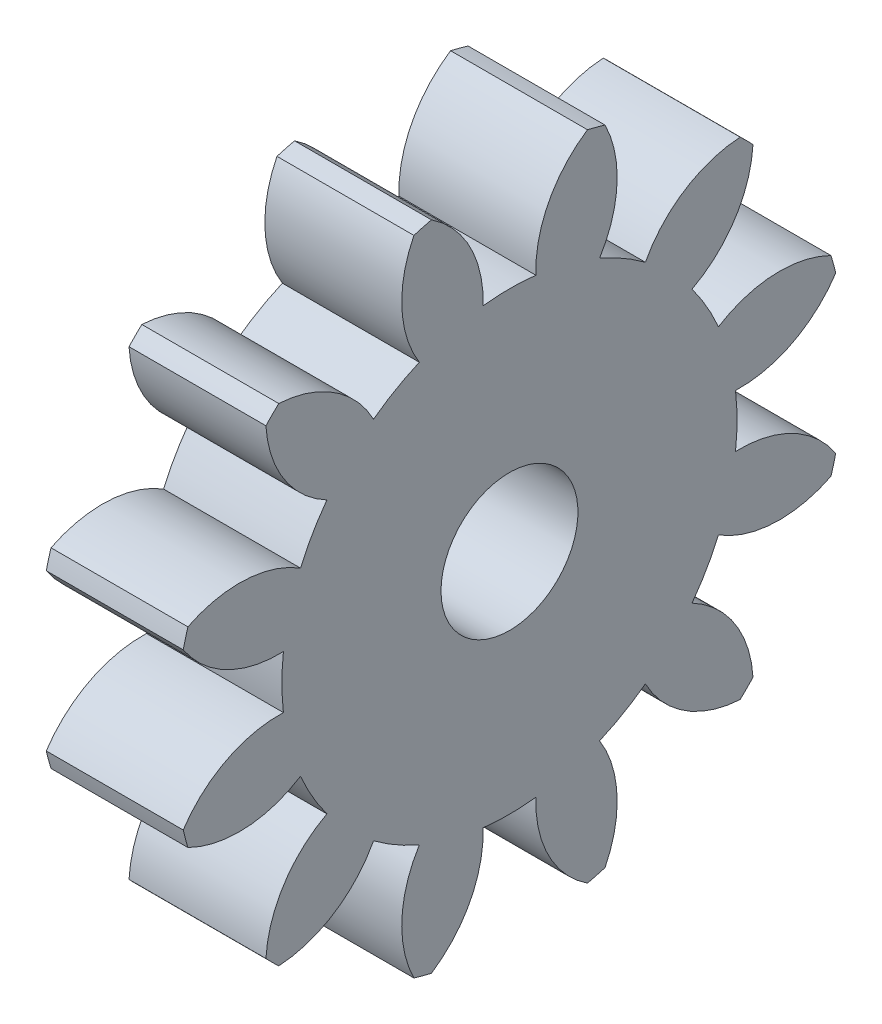
SolidWorks part; units mm, degrees
ref_plane "Plane1" through (0, 0, 0) normal (0, 0, 1) x (1, 0, 0)
ref_plane "Plane2" through (0, 0, 0) normal (0, 1, 0) x (1, 0, 0)
ref_plane "Plane3" through (0, 0, 0) normal (1, 0, 0) x (0, 0, -1)
other "Configuration Table"
sketch "HoldingSke" plane through (0, 0, 0) normal (0, 1, 0) x (1, 0, 0)
  line L0 (0, 0) -> (0.5589, -0.1188)
  line L1 (-15, 0) -> (100, 0) construction
  line L2 (0, 0) -> (-2.1039, 2.3779)
  line L3 (0, 0) -> (-11.863, 4.5341)
  line L4 (0, 0) -> (8.4473, 1.7955)
  line L5 (0, 0) -> (-46.8476, -17.4728)
  line L6 (0, 0) -> (-4.1448, -2.7965)
  line L7 (-2.1039, 2.3779) -> (8.6586, 51.2059)
  line L8 (-76.2, 54.61) -> (-75.3, 54.61)
  line L9 (-71.009, 38.7566) -> (-53.1078, 45.2721)
  line L10 (-76.2, 71.12) -> (104.1128, 71.12)
  line L11 (0, 0) -> (-5, 0)
  line L12 (-76.2, 101.6) -> (-76.147, 101.6)
  line L13 (24.9733, 27.94) -> (52.9518, 28.4284)
  line L14 (24.9733, 27.94) -> (24.9743, 27.94)
  line L15 (24.9733, 27.94) -> (100.4006, 29.5858)
  line L16 (-63.627, -1.75) -> (-12.827, -1.75)
  circle A0 centre (0, 0) radius 2.5
  circle A1 centre (0, 0) radius 8.3115
  circle A2 centre (0, 0) radius 37.5
  circle A3 centre (0, 0) radius 2.5
  dimension "MHD" = 16.623
  dimension "Hub_dia" = 75
  dimension "Bore" = 5
  dimension "MBD" = 5
  dimension "Num_teeth" = 12
  dimension "Pitch" = 0.5714
  dimension "Overall_len" = 50
  dimension "Show_teeth" = 12
  dimension "Thickness" = 5
  dimension "OAL" = 50.0001
  dimension "T_dim" = 0.9
  dimension "Ap" = 20
  dimension "H" = 19.05
  dimension "Pitch_radius" = 180.3128
  dimension "Width" = 5
  dimension "Backlash" = 0.053
  dimension "Addendum_fac" = 1
  dimension "Dedendum_fac" = 1.25
  dimension "Clearance_fac" = 0.25
  dimension "Dedendum_add" = 0.001
  dimension "Module" = 1.75
sketch "BasProSke" plane through (0, 0, 0) normal (0, 1, 0) x (1, 0, 0)
  line L0 (-10, 0) -> (60, 0) construction
  line L1 (0, 0) -> (0, 12.25)
  line L2 (0, 0) -> (5, 0)
  line L3 (5, 0) -> (5, 12.25)
  line L4 (5, 12.25) -> (0, 12.25)
  dimension "Thickness" = 5
  dimension "Diameter" = 24.5
revolve "Base-Revolve" add sketch "BasProSke" angle 360 about L0
sketch "TooCutSke" plane through (0, 0, 0) normal (1, 0, 0) x (0, 0, -1)
  line L1 (0, 0) -> (0, 107) construction
  line L2 (0, 0) -> (-1.4632, 10.3976) construction
  line L3 (0, 0) -> (-5.3948, 20.1337) construction
  line L4 (-1.4632, 10.3976) -> (-2.6974, 10.0668) construction
  arc A0 (0.9651, 8.2553) -> (-0.9651, 8.2553) centre (0, 0) ccw
  arc A1 (2.8783, 11.9332) -> (-2.8783, 11.9332) centre (0, 0) ccw
  circle A2 centre (0, 0) radius 10.5 construction
  circle A3 centre (0, 0) radius 9.8668 construction
  arc A4 (-0.9651, 8.2553) -> (-2.8783, 11.9332) centre (-5.1623, 8.4085) ccw
  arc A5 (2.8783, 11.9332) -> (0.9651, 8.2553) centre (5.1623, 8.4085) ccw
  dimension "Root_dia" = 16.623
  dimension "Overcut_dia" = 24.5508
  dimension "Pitch_dia" = 21
  dimension "Base_dia" = 19.7335
  dimension "Flank_rad" = 4.2
  dimension "Half_ang" = 15
  dimension "Half_CT" = 1.2778
extrude "ToothCut" cut sketch "TooCutSke" along normal through all
fillet "Breaks" [suppressed] radius 0.035
fillet "RootFillets" [suppressed] radius 0.4385
pattern_circular "TeethCuts" count 12 every 30 about axis through (-10, 0, 0) along (1, 0, 0) of "ToothCut", "RootFillets", "Breaks"
sketch "HubNeaOneSke" plane through (0, 0, 0) normal (-1, 0, 0) x (0, 0, 1)
  circle A0 centre (0, 0) radius 8.3115
  dimension "Diameter" = 16.623
extrude "HubNearOne" [suppressed] add sketch "HubNeaOneSke" along normal blind 45.0001
sketch "HubNeaBotSke" plane through (0, 0, 0) normal (-1, 0, 0) x (0, 0, 1)
  circle A0 centre (0, 0) radius 8.3115
  dimension "Diameter" = 16.623
extrude "HubNearBoth" [suppressed] add sketch "HubNeaBotSke" along normal blind 22.5
ref_plane "FarPln" through (5, 0, 0) normal (1, 0, 0) x (0, 0, -1)
sketch "HubFarSke" plane through (5, 0, 0) normal (1, 0, 0) x (0, 0, -1)
  circle A0 centre (0, 0) radius 8.3115
  dimension "Diameter" = 16.623
extrude "HubFar" [suppressed] add sketch "HubFarSke" along normal blind 22.5
sketch "BorSke" plane through (0, 0, 0) normal (1, 0, 0) x (0, 0, -1)
  circle A0 centre (0, 0) radius 2.5
  dimension "Diameter" = 5
extrude "Bore" cut sketch "BorSke" along normal mid plane 100.0001
sketch "KeySke" plane through (0, 0, 0) normal (1, 0, 0) x (0, 0, -1)
  line L0 (-1, 0) -> (-1, 3.4)
  line L1 (-1, 3.4) -> (1, 3.4)
  line L2 (1, 3.4) -> (1, 0)
  line L3 (0, 0) -> (0, 34) construction
  line L4 (-1, 0) -> (1, 0)
  dimension "Offset" = 3.4
  dimension "Width" = 2
extrude "Keyway" [suppressed] cut sketch "KeySke" along normal mid plane 100.0001
pattern_circular "Keyway2" [suppressed] count 2 every 90 about axis through (-10, 0, 0) along (1, 0, 0)
equation "' \"Module@HoldingSke\" = 6.35"
equation "' \"Num_teeth@HoldingSke\" = 12"
equation "' \"Ap@HoldingSke\" =  20"
equation "' \"Ap@HoldingSke\" = 20"
equation "' \"Width@HoldingSke\" = 0.5 * 25.4"
equation "' \"Hub_dia@HoldingSke\"= 1 * 25.4"
equation "' \"Hub_dia@HoldingSke\" = 1 * 25.4"
equation "' \"Overall_len@HoldingSke\" = 1.0 * 25.4"
equation "' \"Bore@HoldingSke\" = 0.75 * 25.4"
equation "' \"T_dim@HoldingSke\" = 0.1 * 25.4"
equation "' \"Width@KeySke\" = 0.25 * 25.4"
equation "' \"Show_teeth@HoldingSke\" = 13"
equation "' \"Backlash@HoldingSke\" = 0.009 * 25.4"
equation "' \"Addendum_fac@HoldingSke\" = 1.0"
equation "' \"Dedendum_fac@HoldingSke\" = 1.25"
equation "' \"Dedendum_add@HoldingSke\" = 0.00005 * 25.4"
equation "' \"Clearance_fac@HoldingSke\" = 0.25"
equation "\"Pitch@HoldingSke\" = 1 / \"Module@HoldingSke\""
equation "\"Overcut_dia@TooCutSke\" = (\"Num_teeth@HoldingSke\" + 2 * \"Addendum_fac@HoldingSke\") / \"Pitch@HoldingSke\" + 0.002 * 25.4"
equation "\"Pitch_dia@TooCutSke\" = \"Num_teeth@HoldingSke\" / \"Pitch@HoldingSke\""
equation "\"Base_dia@TooCutSke\" = \"Num_teeth@HoldingSke\" / \"Pitch@HoldingSke\" * cos((\"Ap@HoldingSke\"  * 3.14159265 / 180))"
equation "\"Root_dia@TooCutSke\" = (\"Num_teeth@HoldingSke\" + 2) / \"Pitch@HoldingSke\" - 2 * (\"Addendum_fac@HoldingSke\" + \"Dedendum_fac@HoldingSke\") / \"Pitch@HoldingSke\" - \"Dedendum_add@HoldingSke\" * 2"
equation "\"Half_ang@TooCutSke\" = 180 / \"Num_teeth@HoldingSke\""
equation "\"Half_CT@TooCutSke\" = \"Num_teeth@HoldingSke\" / \"Pitch@HoldingSke\" * sin((3.14159265 / 2 / \"Num_teeth@HoldingSke\")) / 2 - 7 * \"Backlash@HoldingSke\" / 4"
equation "\"Flank_rad@TooCutSke\" = \"Num_teeth@HoldingSke\" / \"Pitch@HoldingSke\" / 5"
equation "\"Radius@RootFillets\" = \"Clearance_fac@HoldingSke\" / \"Pitch@HoldingSke\" + \"Dedendum_add@HoldingSke\""
equation "\"Break_rad@Breaks\" = 0.02 / \"Pitch@HoldingSke\""
equation "\"Thickness@HoldingSke\" = \"Width@HoldingSke\""
equation "\"OAL@HoldingSke\" = \"Thickness@HoldingSke\""
equation "\"MHD@HoldingSke\" = (\"Num_teeth@HoldingSke\" + 2) / \"Pitch@HoldingSke\" - 2 * (\"Addendum_fac@HoldingSke\" + \"Dedendum_fac@HoldingSke\")  / \"Pitch@HoldingSke\" - \"Dedendum_add@HoldingSke\" * 2"
equation "\"MBD@HoldingSke\" = (\"Num_teeth@HoldingSke\" + 2) / \"Pitch@HoldingSke\" - 2 * (\"Addendum_fac@HoldingSke\" + \"Dedendum_fac@HoldingSke\")  / \"Pitch@HoldingSke\" - \"Dedendum_add@HoldingSke\" * 2 - 0.002 * 25.4"
equation "\"MHD@HoldingSke\" = ((sgn( \"MHD@HoldingSke\" - \"Hub_dia@HoldingSke\" )-1)*( \"MHD@HoldingSke\" - \"Hub_dia@HoldingSke\" ))/-2+ \"Hub_dia@HoldingSke\""
equation "\"MBD@HoldingSke\" = ((sgn( \"MBD@HoldingSke\" - \"Bore@HoldingSke\" )-1)*( \"MBD@HoldingSke\" - \"Bore@HoldingSke\" ))/-2+ \"Bore@HoldingSke\""
equation "\"OAL@HoldingSke\" = ((sgn( \"OAL@HoldingSke\" - \"Overall_len@HoldingSke\" )+1)*( \"OAL@HoldingSke\" - \"Overall_len@HoldingSke\" ))/2 + \"Overall_len@HoldingSke\" + 0.000002 * 25.4"
equation "\"Num_teeth@TeethCuts\" = int( \"Show_teeth@HoldingSke\" ) + 1"
equation "\"Num_teeth@TeethCuts\" = ((sgn( \"Num_teeth@TeethCuts\" - \"Num_teeth@HoldingSke\" )-1)*( \"Num_teeth@TeethCuts\" - \"Num_teeth@HoldingSke\" ))/-2+ \"Num_teeth@HoldingSke\""
equation "\"Num_teeth@TeethCuts\" = ((sgn( \"Num_teeth@TeethCuts\" - 2.0)+1)*( \"Num_teeth@TeethCuts\" - 2.0))/2 +2.0"
equation "\"Angle@TeethCuts\" = 360.0 / \"Num_teeth@HoldingSke\""
equation "\"Diameter@BasProSke\" = (\"Num_teeth@HoldingSke\" + 2 * \"Addendum_fac@HoldingSke\") / \"Pitch@HoldingSke\""
equation "\"Thickness@BasProSke\"  = \"Thickness@HoldingSke\""
equation "' \"Fillet_rad@BasProSke\" =  \"Thickness@HoldingSke\" * 0.05"
equation "' \"Fillet_rad@BasProSke\" = \"Thickness@HoldingSke\" * 0.05"
equation "\"MHD@HoldingSke\" = ((sgn( \"MHD@HoldingSke\" - \"Root_dia@TooCutSke\" )-1)*( \"MHD@HoldingSke\" - \"Root_dia@TooCutSke\" ))/-2+ \"Root_dia@TooCutSke\""
equation "\"Diameter@HubNeaOneSke\" = \"MHD@HoldingSke\""
equation "\"Length@HubNearOne\" = \"OAL@HoldingSke\" - \"Thickness@BasProSke\""
equation "\"Diameter@HubNeaBotSke\" = \"MHD@HoldingSke\""
equation "\"Length@HubNearBoth\" = ( \"OAL@HoldingSke\" - \"Thickness@BasProSke\" ) / 2.0"
equation "\"Thickness@FarPln\" = \"Thickness@BasProSke\""
equation "\"Diameter@HubFarSke\" = \"MHD@HoldingSke\""
equation "\"Length@HubFar\" = ( \"OAL@HoldingSke\" - \"Thickness@BasProSke\" ) / 2.0"
equation "\"Diameter@BorSke\" = \"MBD@HoldingSke\""
equation "\"D1@Bore\" = \"OAL@HoldingSke\" * 2.0"
equation "\"D1@Keyway\" = \"OAL@HoldingSke\" * 2.0"
equation "\"Offset@KeySke\" = \"T_dim@HoldingSke\" + \"MBD@HoldingSke\" / 2.0"
